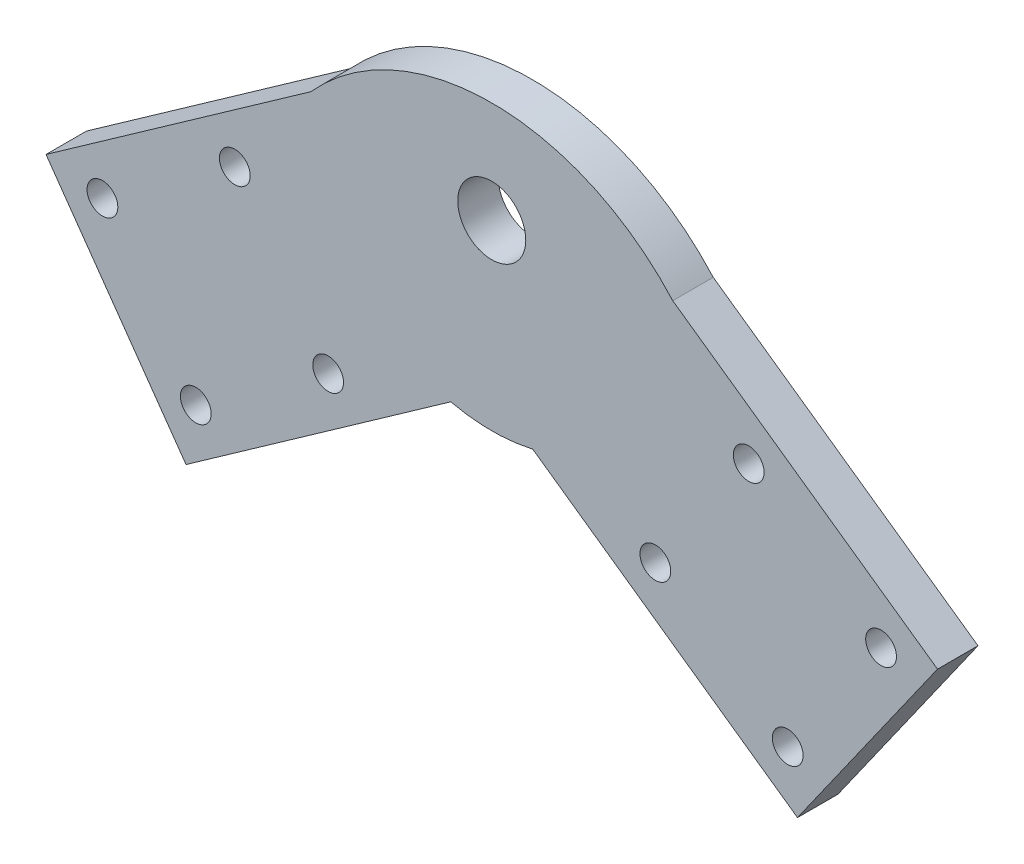
SolidWorks part; units mm, degrees
material "PLA 15%"
ref_plane "Front Plane" through (0, 0, 0) normal (0, 0, 1) x (1, 0, 0)
ref_plane "Top Plane" through (0, 0, 0) normal (0, 1, 0) x (1, 0, 0)
ref_plane "Right Plane" through (0, 0, 0) normal (1, 0, 0) x (0, 0, -1)
sketch "Sketch2" plane through (0, 0, 0) normal (0, 0, 1) x (1, 0, 0)
  line L8 (0, 0) -> (0, -22.5) construction
  line L9 (0, 0) -> (5.0614, -21.9233) construction
  line L10 (0, 0) -> (-5.0614, -21.9233) construction
  line L11 (5.0614, -21.9233) -> (22.35, 2.5941) construction
  line L12 (5.0614, -21.9233) -> (37.7513, -44.9747)
  line L13 (22.35, 2.5941) -> (55.0399, -20.4573)
  line L14 (37.7513, -44.9747) -> (55.0399, -20.4573)
  line L15 (-5.0614, -21.9233) -> (-22.35, 2.5941) construction
  line L16 (-5.0614, -21.9233) -> (-37.7513, -44.9747)
  line L17 (-22.35, 2.5941) -> (-55.0399, -20.4573)
  line L18 (-37.7513, -44.9747) -> (-55.0399, -20.4573)
  line L28 (-36.5465, -38.0071) -> (-20.2016, -26.4814) construction
  line L29 (-12.0291, -20.7185) -> (-23.5548, -4.3735) construction
  line L30 (20.2016, -26.4814) -> (31.7273, -10.1364) construction
  line L32 (31.7273, -10.1364) -> (48.0722, -21.6621) construction
  line L37 (20.2016, -26.4814) -> (36.5465, -38.0071) construction
  line L38 (36.5465, -38.0071) -> (48.0722, -21.6621) construction
  line L39 (-23.5548, -4.3735) -> (-48.0722, -21.6621) construction
  line L40 (-31.7273, -10.1364) -> (-48.0722, -21.6621) construction
  line L42 (-12.0291, -20.7185) -> (-36.5465, -38.0071) construction
  line L43 (-36.5465, -38.0071) -> (-48.0722, -21.6621) construction
  line L45 (-48.0722, -21.6621) -> (-36.5465, -38.0071) construction
  line L46 (-36.5465, -38.0071) -> (-20.2016, -26.4814) construction
  line L47 (-20.2016, -26.4814) -> (-31.7273, -10.1364) construction
  line L48 (-31.7273, -10.1364) -> (-48.0722, -21.6621) construction
  arc A0 (-5.0614, -21.9233) -> (5.0614, -21.9233) centre (0, 0) ccw
  arc A3 (-22.35, 2.5941) -> (-21.0669, -7.9017) centre (0, 0) ccw construction
  arc A4 (-21.0669, -7.9017) -> (-14.517, -17.1903) centre (0, 0) ccw construction
  arc A5 (-14.517, -17.1903) -> (-5.0614, -21.9233) centre (0, 0) ccw construction
  arc A6 (5.0614, -21.9233) -> (14.517, -17.1903) centre (0, 0) ccw construction
  arc A8 (14.517, -17.1903) -> (21.0669, -7.9017) centre (0, 0) ccw construction
  arc A9 (21.0669, -7.9017) -> (22.35, 2.5941) centre (0, 0) ccw construction
  circle A12 centre (0, 0) radius 4.2
  arc A15 (-22.35, 2.5941) -> (22.35, 2.5941) centre (0, -17.4179) cw
  dimension "D5" = 45
  dimension "D8" = 8.4
  dimension "D10" = 30
  dimension "D1" = 13
  dimension "D2" = 13
  dimension "D3" = 30
  dimension "D4" = 30
  dimension "D6" = 40
  dimension "D7" = 40
  dimension "D11" = 20
  dimension "D12" = 20
  dimension "D13" = 5
  dimension "D14" = 5
  dimension "D15" = 5
  dimension "D16" = 20
  dimension "D9" = 5
extrude "Boss-Extrude1" add sketch "Sketch2" along normal blind 5
hole_wizard "M3 Clearance Hole1" positions "Sketch8" profile "Sketch9" hole size "M3" standard "ANSI Metric" end condition through all
sketch "Sketch8" plane through (0, 0, 5) normal (0, 0, 1) x (1, 0, 0)
  point P24 (-31.7273, -10.1364)
  point P27 (-20.2016, -26.4814)
  point P30 (-36.5465, -38.0071)
  point P33 (-48.0722, -21.6621)
  point P36 (31.7273, -10.1364)
  point P39 (48.0722, -21.6621)
  point P42 (20.2016, -26.4814)
  point P45 (36.5465, -38.0071)
sketch "Sketch9" plane through (-31.7273, -10.1364, 5) normal (1, 0, 0) x (0, -1, 0)
  line L0 (0, 0) -> (0, 5)
  line L1 (0, 5) -> (1.9, 5)
  line L2 (1.9, 5) -> (1.9, 0)
  line L5 (1.9, 0) -> (0, 0)
  line L11 (0, -6.35) -> (0, 107.95) construction
  dimension "Thru Hole Dia." = 3.8
  dimension "Thru Hole Depth" = 5
